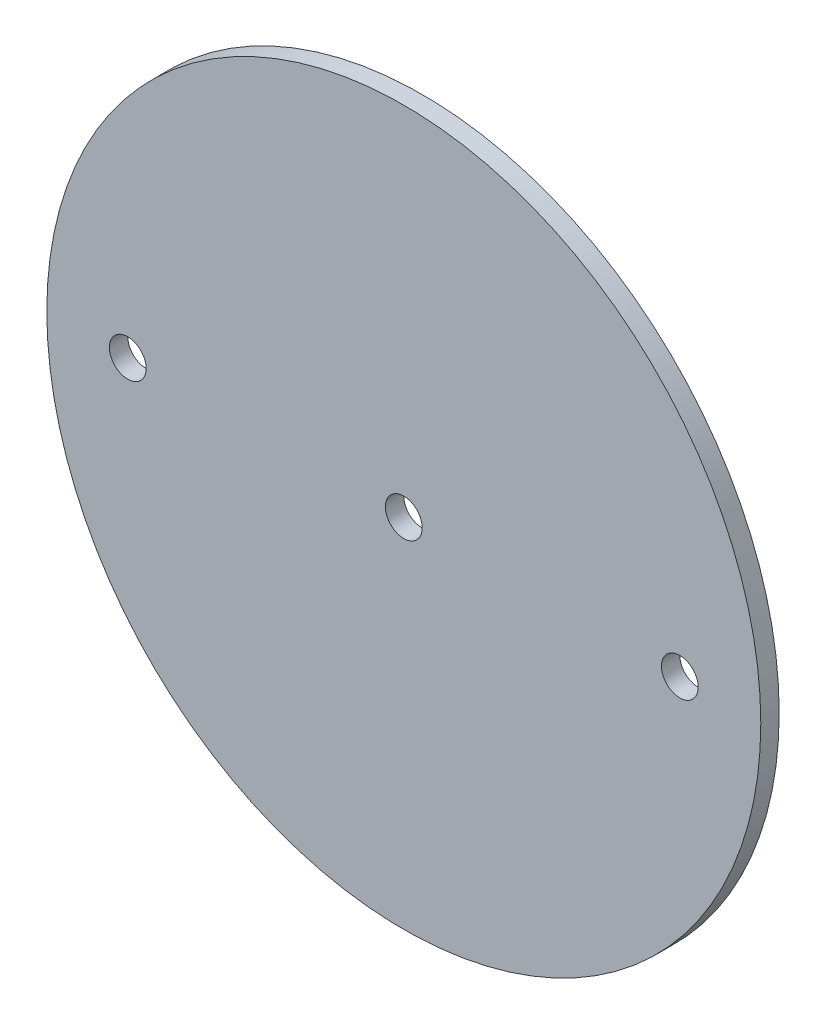
SolidWorks part; units mm, degrees
ref_plane "Front Plane" through (0, 0, 0) normal (0, 0, 1) x (1, 0, 0)
ref_plane "Top Plane" through (0, 0, 0) normal (0, 1, 0) x (1, 0, 0)
ref_plane "Right Plane" through (0, 0, 0) normal (1, 0, 0) x (0, 0, -1)
sketch "Sketch1" plane through (0, 0, 0) normal (0, 0, 1) x (1, 0, 0)
  circle A0 centre (0, 0) radius 61.595
  dimension "D1" = 123.19
extrude "Boss-Extrude1" add sketch "Sketch1" along normal mid plane 3.175
sketch "Sketch2" plane through (0, 0, 1.5875) normal (0, 0, 1) x (1, 0, 0)
  line L0 (-1000, 0) -> (49000, 0) construction
  point P1 (0, 0)
  point P4 (47.625, 0)
  point P5 (-47.625, 0)
  dimension "D1" = 47.625
  dimension "D2" = 95.25
hole_wizard "1/4 (0.25) Diameter Hole1" positions "Sketch2" profile "Sketch3" hole size "1/4" standard "ANSI Inch" end condition through all
sketch "Sketch3" plane through (-47.625, 0, 1.5875) normal (1, 0, 0) x (0, -1, 0)
  line L0 (0, 0) -> (0, 3.175)
  line L1 (0, 3.175) -> (3.175, 3.175)
  line L2 (3.175, 3.175) -> (3.175, 0)
  line L5 (3.175, 0) -> (0, 0)
  line L11 (0, -6.35) -> (0, 107.95) construction
  dimension "Thru Hole Dia." = 6.35
  dimension "Thru Hole Depth" = 3.175
equation "\"AIRFRAME_OD\"= 5.15in"
equation "\"AIRFRAME_ID\"= 4.99in"
equation "\"FLAT_T\"= 0.125in"
equation "\"NOSE_EXP_L\"= 27in"
equation "\"NOSE_SHOULDER_L\"= 5in"
equation "\"MAIN_L\"= 30in"
equation "\"RECO_COUP_L\"= 10in"
equation "\"RECO_SWITCH_L\"= 2in"
equation "\"DROGUE_L\"= 20in"
equation "\"ATS_FORE_COUP_L\"= 5.5in"
equation "\"ATS_AFT_COUP_L\"= 4.5in"
equation "\"LOWER_L\"= 30in"
equation "\"FIN_N\"= 4"
equation "\"CR_AFT_X\"= 0.5in"
equation "\"CR_FORE_X\"= 9.25in"
equation "\"FIN_ROOT\"= 8in"
equation "\"FIN_X\"= 0.75in"
equation "\"MOTOR_OD\"= 3.091in"
equation "\"MOTOR_ID\"= 3.00in"
equation "\"COUPLER_OD\"= 4.998in"
equation "\"COUPLER_ID\"= 4.85in"
equation "\"D1@Sketch1\"=\"COUPLER_ID\""
equation "\"D1@Boss-Extrude1\"=\"FLAT_T\""
equation "\"RECO_ROD_X\"= 3.5in"
equation "\"ATS_ROD_X\"= 3.75in"
equation "\"D1@Sketch2\"=\"ATS_ROD_X\"*0.5"
equation "\"D2@Sketch2\"=\"ATS_ROD_X\""
equation "\"MOTOR_L\"= 14in"
equation "\"MOTOR_LOWER_X\"= 2in"
